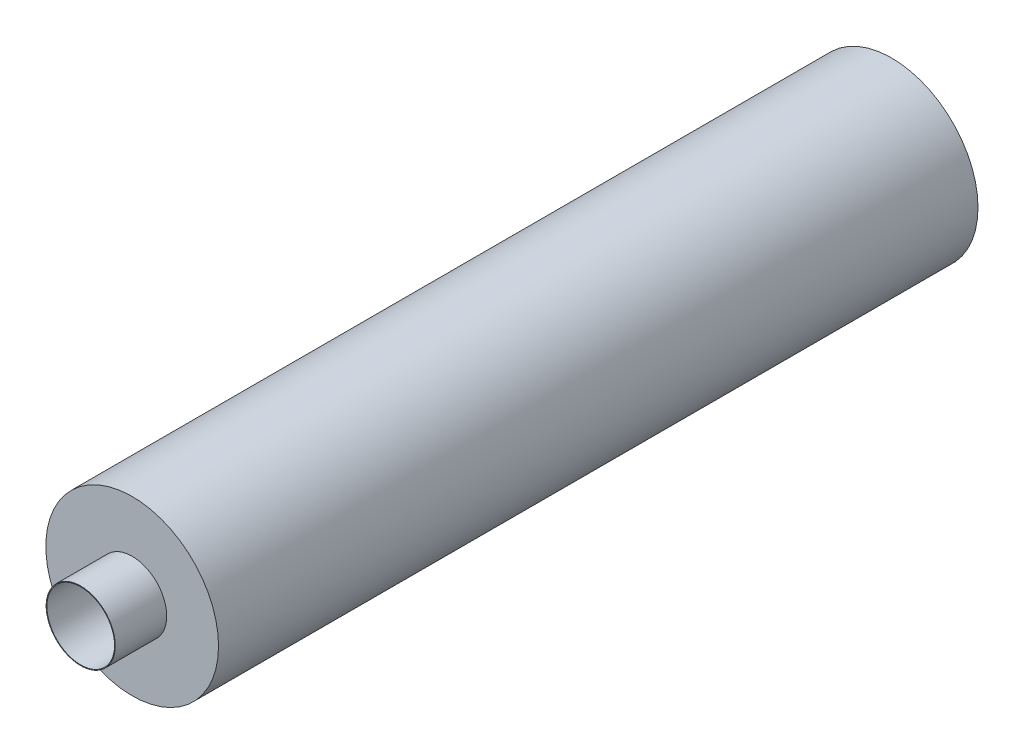
SolidWorks part; units mm, degrees
ref_plane "Front Plane" through (0, 0, 0) normal (0, 0, 1) x (1, 0, 0)
ref_plane "Top Plane" through (0, 0, 0) normal (0, 1, 0) x (1, 0, 0)
ref_plane "Right Plane" through (0, 0, 0) normal (1, 0, 0) x (0, 0, -1)
sketch "Sketch1" plane through (0, 0, 0) normal (0, 0, 1) x (1, 0, 0)
  circle A0 centre (0, 0) radius 250
  dimension "D1" = 500
extrude "Boss-Extrude1" add sketch "Sketch1" along normal blind 2198
shell "Shell2" thickness 2
sketch "Sketch2" plane through (0, 0, 2198) normal (0, 0, 1) x (1, 0, 0)
  circle A0 centre (0, 0) radius 100
  circle A1 centre (0, 0) radius 248 construction
  circle A2 centre (0, 0) radius 248
  dimension "D1" = 200
extrude "Extrude-Thin1" add sketch "Sketch2" along normal blind 150 separate body thin contours A0
sketch "Sketch3" plane through (0, 0, 2198) normal (0, 0, 1) x (1, 0, 0)
  circle A0 centre (0, 0) radius 250
  circle A1 centre (0, 0) radius 98 construction
  circle A2 centre (0, 0) radius 98
extrude "Boss-Extrude2" add sketch "Sketch3" along normal blind 1
